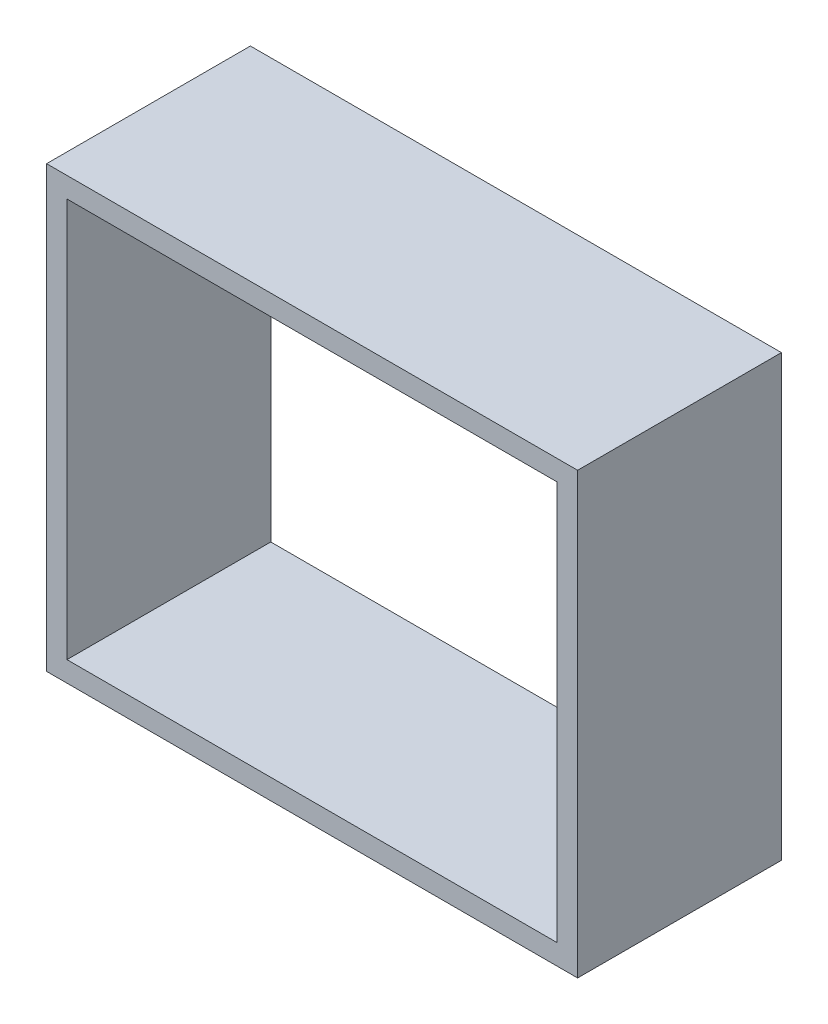
SolidWorks part; units mm, degrees
ref_plane "Front Plane" through (0, 0, 0) normal (0, 0, 1) x (1, 0, 0)
ref_plane "Top Plane" through (0, 0, 0) normal (0, 1, 0) x (1, 0, 0)
ref_plane "Right Plane" through (0, 0, 0) normal (1, 0, 0) x (0, 0, -1)
sketch "Sketch1" plane through (0, 0, 0) normal (0, 0, 1) x (1, 0, 0)
  line L0 (-32.7273, 70.5301) -> (97.5564, 70.5301)
  line L1 (-32.7273, 70.5301) -> (-32.7273, -37.3485)
  line L2 (97.5564, 70.5301) -> (97.5564, -37.3485)
  line L3 (-32.7273, -37.3485) -> (97.5564, -37.3485)
  line L4 (-27.7273, 65.5301) -> (92.5564, 65.5301)
  line L5 (-27.7273, 65.5301) -> (-27.7273, -32.3485)
  line L6 (92.5564, 65.5301) -> (92.5564, -32.3485)
  line L7 (-27.7273, -32.3485) -> (92.5564, -32.3485)
  line L8 (32.4146, 70.5301) -> (32.4146, -37.3485) construction
  line L9 (-32.7273, 16.5908) -> (97.5564, 16.5908) construction
  point P12 (92.5564, 65.5301)
  dimension "D1" = 5
  dimension "D2" = 5
extrude "Boss-Extrude1" add sketch "Sketch1" along normal blind 50
